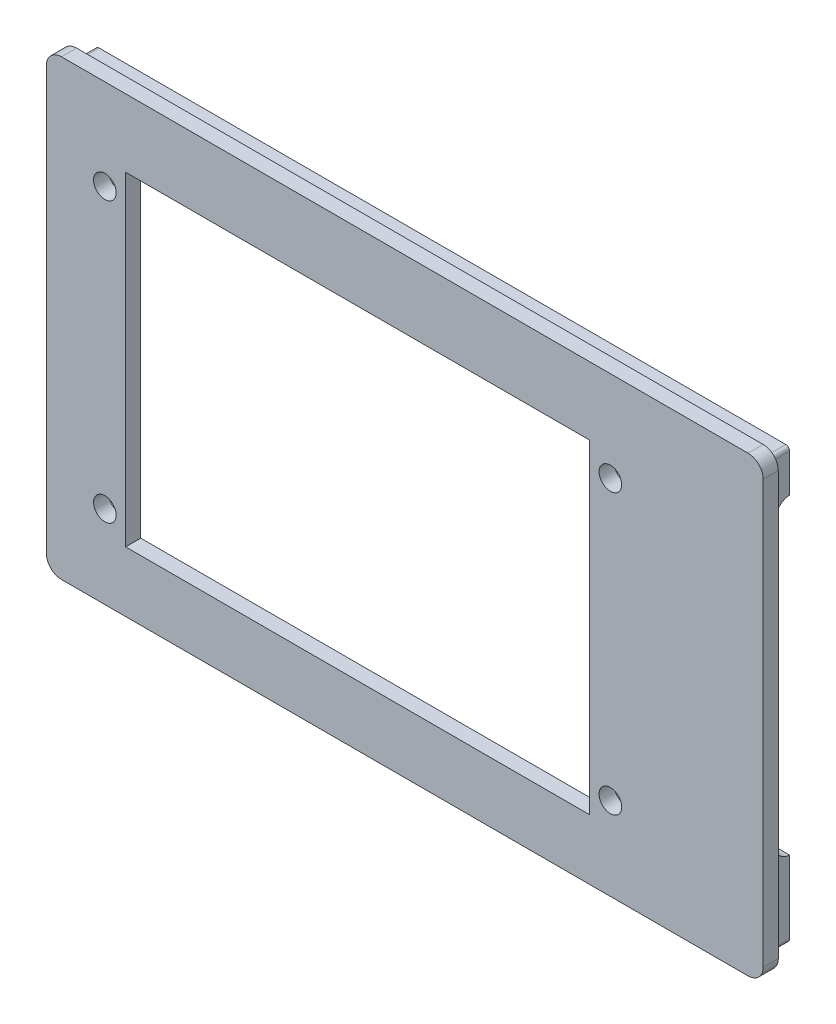
SolidWorks part; units mm, degrees
ref_plane "Top" through (0, 0, 0) normal (0, 0, 1) x (1, 0, 0)
ref_plane "Front" through (0, 0, 0) normal (0, 1, 0) x (1, 0, 0)
ref_plane "Right Plane" through (0, 0, 0) normal (1, 0, 0) x (0, 0, -1)
sketch "Sketch1" plane through (0, 0, 0) normal (0, 0, 1) x (1, 0, 0)
  line L1 (2, 0) -> (93, 0)
  line L2 (0, 2) -> (0, 58)
  line L3 (2, 60) -> (93, 60)
  line L4 (95, 2) -> (95, 58)
  line L5 (10.5, 51) -> (72, 51)
  line L6 (10.5, 51) -> (10.5, 8)
  line L7 (10.5, 8) -> (72, 8)
  line L8 (72, 51) -> (72, 8)
  arc A0 (93, 60) -> (95, 58) centre (93, 58) cw
  arc A1 (93, 0) -> (95, 2) centre (93, 2) ccw
  arc A2 (2, 0) -> (0, 2) centre (2, 2) cw
  arc A3 (0, 58) -> (2, 60) centre (2, 58) cw
  point P9 (95, 0)
  point P12 (0, 0)
  dimension "D3" = 2
  dimension "D1" = 95
  dimension "D2" = 60
  dimension "D4" = 61.5
  dimension "D5" = 43
  dimension "D6" = 8
  dimension "D7" = 23
extrude "Boss-Extrude1" add sketch "Sketch1" along normal blind 2
sketch "Sketch2" plane through (0, 0, 0) normal (0, 0, -1) x (-1, 0, 0)
  line L8 (-92, 57) -> (-92, 3)
  line L9 (-92, 3) -> (-3, 3)
  line L10 (-3, 3) -> (-3, 57)
  line L11 (-3, 57) -> (-92, 57)
  line L16 (-93.5, 58) -> (-93.5, 2)
  line L17 (-93, 1.5) -> (-2, 1.5)
  line L18 (-1.5, 2) -> (-1.5, 58)
  line L19 (-2, 58.5) -> (-93, 58.5)
  line L20 (-93.5, 58) -> (-93.5, 2)
  line L21 (-93, 1.5) -> (-2, 1.5)
  line L22 (-1.5, 2) -> (-1.5, 58)
  line L23 (-2, 58.5) -> (-93, 58.5)
  arc A4 (-92, 3) -> (-92, 3) centre (-92, 3) ccw
  arc A5 (-3, 3) -> (-3, 3) centre (-3, 3) ccw
  arc A6 (-3, 57) -> (-3, 57) centre (-3, 57) ccw
  arc A7 (-92, 57) -> (-92, 57) centre (-92, 57) ccw
  arc A8 (-93, 58.5) -> (-93.5, 58) centre (-93, 58) ccw
  arc A9 (-93.5, 2) -> (-93, 1.5) centre (-93, 2) ccw
  arc A10 (-2, 1.5) -> (-1.5, 2) centre (-2, 2) ccw
  arc A11 (-1.5, 58) -> (-2, 58.5) centre (-2, 58) ccw
  arc A12 (-93, 58.5) -> (-93.5, 58) centre (-93, 58) ccw
  arc A13 (-93.5, 2) -> (-93, 1.5) centre (-93, 2) ccw
  arc A14 (-2, 1.5) -> (-1.5, 2) centre (-2, 2) ccw
  arc A15 (-1.5, 58) -> (-2, 58.5) centre (-2, 58) ccw
  dimension "D1" = 1.5
  dimension "D2" = 1.5
extrude "Boss-Extrude2" add sketch "Sketch2" along normal blind 3
sketch "Sketch3" plane through (0, 0, 2) normal (0, 0, 1) x (1, 0, 0)
  line L1 (10.5, 51) -> (10.5, 8) construction
  line L3 (72, 51) -> (10.5, 51) construction
  circle A0 centre (7.75, 48) radius 1.5
  circle A1 centre (74.75, 48) radius 1.5
  circle A2 centre (7.75, 11) radius 1.5
  circle A3 centre (74.75, 11) radius 1.5
  dimension "D5" = 3
  dimension "D1" = 67
  dimension "D2" = 67
  dimension "D3" = 37
  dimension "D4" = 37
  dimension "D6" = 3
  dimension "D7" = 2.75
extrude "Cut-Extrude1" cut sketch "Sketch3" against normal up to next
sketch "Sketch4" plane through (93.5, 0, 0) normal (1, 0, 0) x (0, 0, -1)
  line L1 (6.3585, 11.6212) -> (3.0915, 11.6212)
  line L2 (8.3585, 13.6212) -> (8.3585, 50.9419)
  line L3 (6.3585, 52.9419) -> (3.0915, 52.9419)
  line L4 (1.0915, 13.6212) -> (1.0915, 50.9419)
  arc A0 (3.0915, 52.9419) -> (1.0915, 50.9419) centre (3.0915, 50.9419) ccw
  arc A1 (3.0915, 11.6212) -> (1.0915, 13.6212) centre (3.0915, 13.6212) cw
  arc A2 (8.3585, 50.9419) -> (6.3585, 52.9419) centre (6.3585, 50.9419) ccw
  arc A3 (6.3585, 11.6212) -> (8.3585, 13.6212) centre (6.3585, 13.6212) ccw
  dimension "D1" = 2
  dimension "D2" = 2
extrude "Cut-Extrude2" cut sketch "Sketch4" against normal up to next
